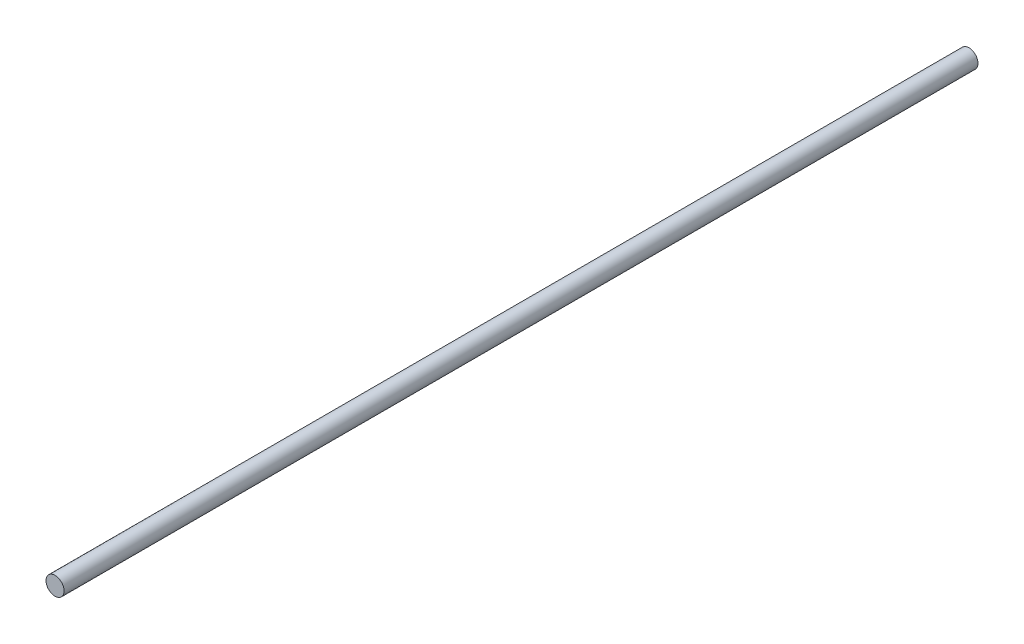
SolidWorks part; units mm, degrees
ref_plane "Front Plane" through (0, 0, 0) normal (0, 0, 1) x (1, 0, 0)
ref_plane "Top Plane" through (0, 0, 0) normal (0, 1, 0) x (1, 0, 0)
ref_plane "Right Plane" through (0, 0, 0) normal (1, 0, 0) x (0, 0, -1)
sketch "Sketch1" plane through (0, 0, 0) normal (0, 0, 1) x (1, 0, 0)
  circle A0 centre (0, 0) radius 2
  dimension "D1" = 4
extrude "Boss-Extrude1" add sketch "Sketch1" along normal blind 201.85
